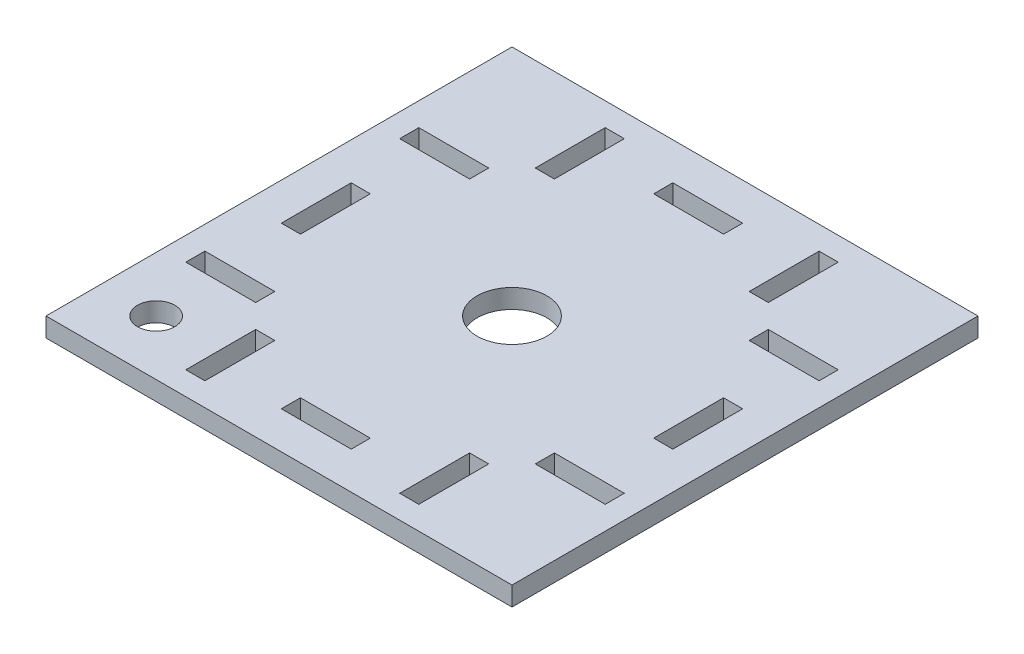
SolidWorks part; units mm, degrees
material "Corrugated Paper"
ref_plane "Front Plane" through (0, 0, 0) normal (0, 0, 1) x (1, 0, 0)
ref_plane "Top Plane" through (0, 0, 0) normal (0, 1, 0) x (1, 0, 0)
ref_plane "Right Plane" through (0, 0, 0) normal (1, 0, 0) x (0, 0, -1)
sketch "Sketch1" plane through (0, 0, 0) normal (0, 1, 0) x (1, 0, 0)
  line L0 (-20.9, 30) -> (-25, 30)
  line L1 (-50, -50) -> (50, -50)
  line L2 (-50, -50) -> (-50, 50)
  line L3 (-50, 50) -> (50, 50)
  line L4 (50, -50) -> (50, 50)
  line L5 (-50, -50) -> (50, 50) construction
  line L6 (-50, 50) -> (50, -50) construction
  line L7 (-30, 30) -> (30, 30) construction
  line L8 (-30, 30) -> (-30, -30) construction
  line L9 (-30, -30) -> (30, -30) construction
  line L10 (30, 30) -> (30, -30) construction
  line L11 (-30, 20.9) -> (-45, 20.9)
  line L12 (-30, 20.9) -> (-30, 25)
  line L13 (-30, 25) -> (-45, 25)
  line L14 (-45, 20.9) -> (-45, 25)
  line L15 (-25, 30) -> (-25, 45)
  line L16 (-20.9, 45) -> (-25, 45)
  line L17 (-20.9, 30) -> (-20.9, 45)
  line L18 (30, -20.9) -> (30, -25)
  line L19 (45, -20.9) -> (45, -25)
  line L20 (30, -25) -> (45, -25)
  line L21 (30, -20.9) -> (45, -20.9)
  line L22 (20.9, -30) -> (25, -30)
  line L23 (25, -30) -> (25, -45)
  line L24 (20.9, -45) -> (25, -45)
  line L25 (20.9, -30) -> (20.9, -45)
  line L26 (0, -50) -> (0, 50) construction
  line L27 (50, 0) -> (-50, 0) construction
  line L28 (45, 20.9) -> (45, 25)
  line L29 (30, 25) -> (45, 25)
  line L30 (30, 20.9) -> (30, 25)
  line L31 (30, 20.9) -> (45, 20.9)
  line L32 (-30, -20.9) -> (-30, -25)
  line L33 (-45, -20.9) -> (-45, -25)
  line L34 (-30, -25) -> (-45, -25)
  line L35 (-30, -20.9) -> (-45, -20.9)
  line L36 (20.9, 45) -> (25, 45)
  line L37 (25, 30) -> (25, 45)
  line L38 (20.9, 30) -> (25, 30)
  line L39 (20.9, 30) -> (20.9, 45)
  line L40 (-20.9, -30) -> (-25, -30)
  line L41 (-20.9, -45) -> (-25, -45)
  line L42 (-20.9, -30) -> (-20.9, -45)
  line L43 (-25, -30) -> (-25, -45)
  line L44 (-7.5, 42) -> (-20.9, 42) construction
  line L45 (-7.5, 42) -> (7.5, 42)
  line L46 (-7.5, 42) -> (-7.5, 37.9)
  line L47 (-7.5, 37.9) -> (7.5, 37.9)
  line L48 (7.5, 42) -> (7.5, 37.9)
  line L49 (7.5, 42) -> (20.9, 42) construction
  line L50 (7.5, -42) -> (7.5, -37.9)
  line L51 (-7.5, -42) -> (-7.5, -37.9)
  line L52 (-7.5, -37.9) -> (7.5, -37.9)
  line L53 (-7.5, -42) -> (7.5, -42)
  line L54 (42, 7.5) -> (37.9, 7.5)
  line L55 (-37.9, -7.5) -> (-37.9, 7.5)
  line L56 (-42, -7.5) -> (-37.9, -7.5)
  line L57 (-42, -7.5) -> (-42, 7.5)
  line L58 (-42, 7.5) -> (-37.9, 7.5)
  line L59 (42, -7.5) -> (37.9, -7.5)
  line L60 (42, -7.5) -> (42, 7.5)
  line L61 (37.9, -7.5) -> (37.9, 7.5)
  circle A0 centre (0, 0) radius 7.5
  circle A1 centre (-38.1838, -38.1838) radius 4
  point P0 (0, 0)
  dimension "D10" = 15
  dimension "D11" = 8
  dimension "D1" = 100
  dimension "D2" = 100
  dimension "D3" = 30
  dimension "D4" = 15
  dimension "D5" = 4.1
  dimension "D6" = 50
  dimension "D7" = 4.1
  dimension "D8" = 15
  dimension "D9" = 8
extrude "Boss-Extrude1" add sketch "Sketch1" along normal blind 4.1
